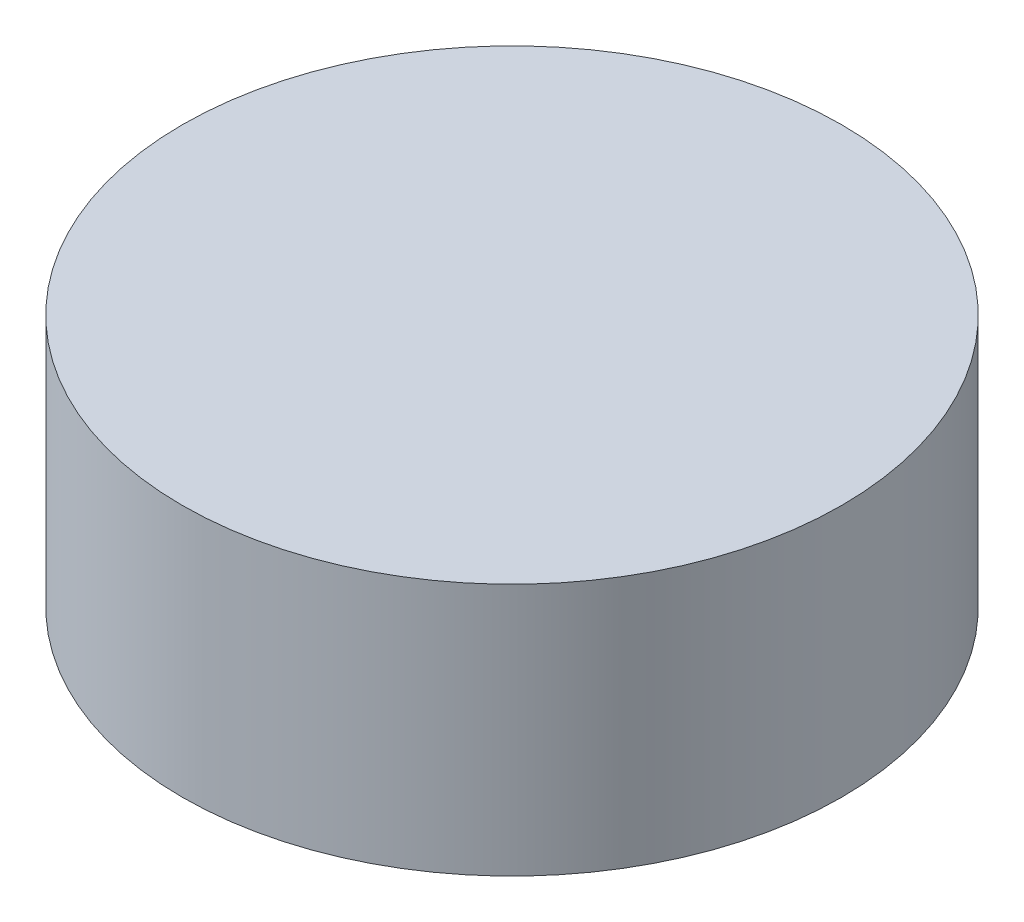
SolidWorks part; units mm, degrees
ref_plane "Спереди" through (0, 0, 0) normal (0, 0, 1) x (1, 0, 0)
ref_plane "Сверху" through (0, 0, 0) normal (0, 1, 0) x (1, 0, 0)
ref_plane "Справа" through (0, 0, 0) normal (1, 0, 0) x (0, 0, -1)
other "Configuration Table"
sketch "Sketch1" plane through (0, 0, 0) normal (0, 1, 0) x (1, 0, 0)
  circle A0 centre (0, 0) radius 30
  dimension "D1" = 60
extrude "Boss-Extrude1" add sketch "Sketch1" along normal blind 23
